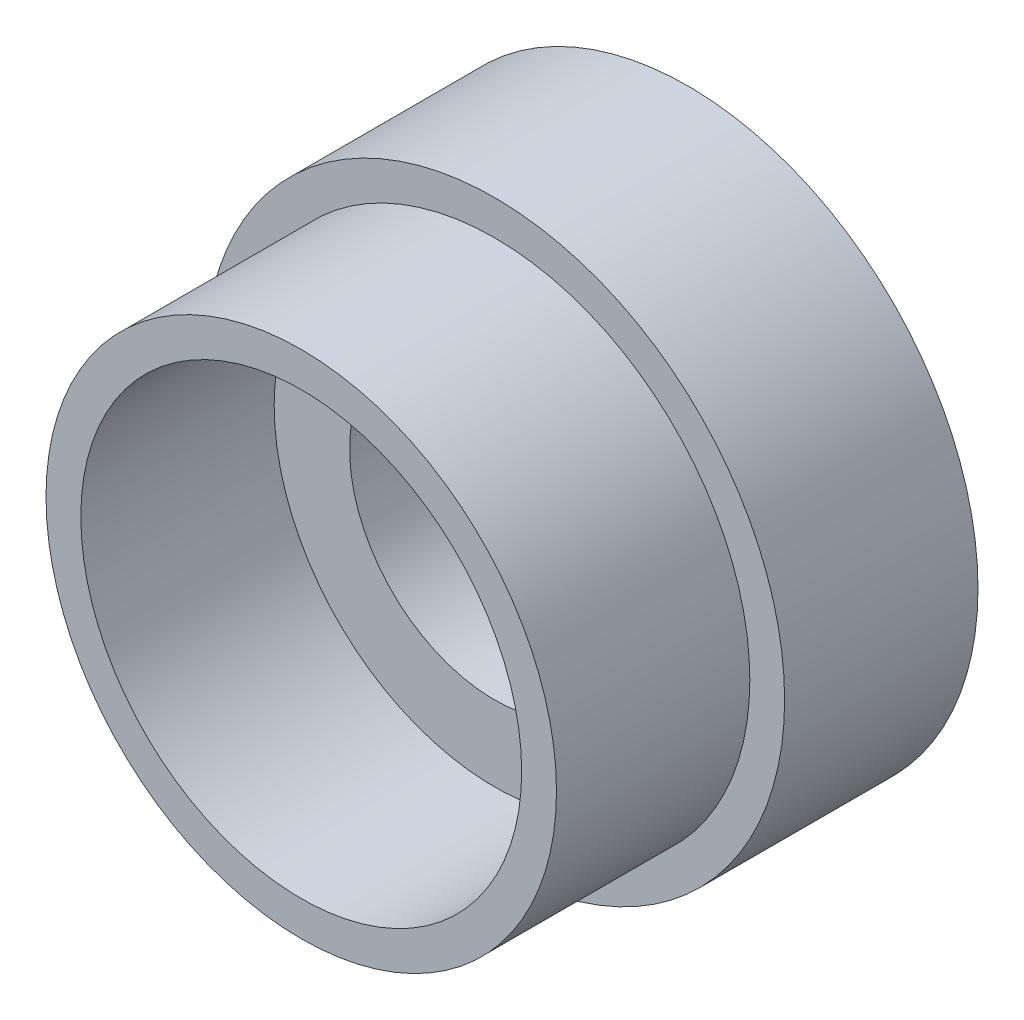
SolidWorks part; units mm, degrees
ref_plane "Front Plane" through (0, 0, 0) normal (0, 0, 1) x (1, 0, 0)
ref_plane "Top Plane" through (0, 0, 0) normal (0, 1, 0) x (1, 0, 0)
ref_plane "Right Plane" through (0, 0, 0) normal (1, 0, 0) x (0, 0, -1)
sketch "Sketch1" plane through (0, 0, 0) normal (0, 0, 1) x (1, 0, 0)
  circle A0 centre (0, 0) radius 9.525
  circle A1 centre (0, 0) radius 4.7625
extrude "Boss-Extrude1" add sketch "Sketch1" along normal blind 6.35
sketch "Sketch2" plane through (0, 0, 6.35) normal (0, 0, 1) x (1, 0, 0)
  circle A1 centre (0, 0) radius 8.382
  circle A2 centre (0, 0) radius 7.239
  dimension "D1" = 1.143
extrude "Boss-Extrude3" add sketch "Sketch2" along normal blind 6.35
